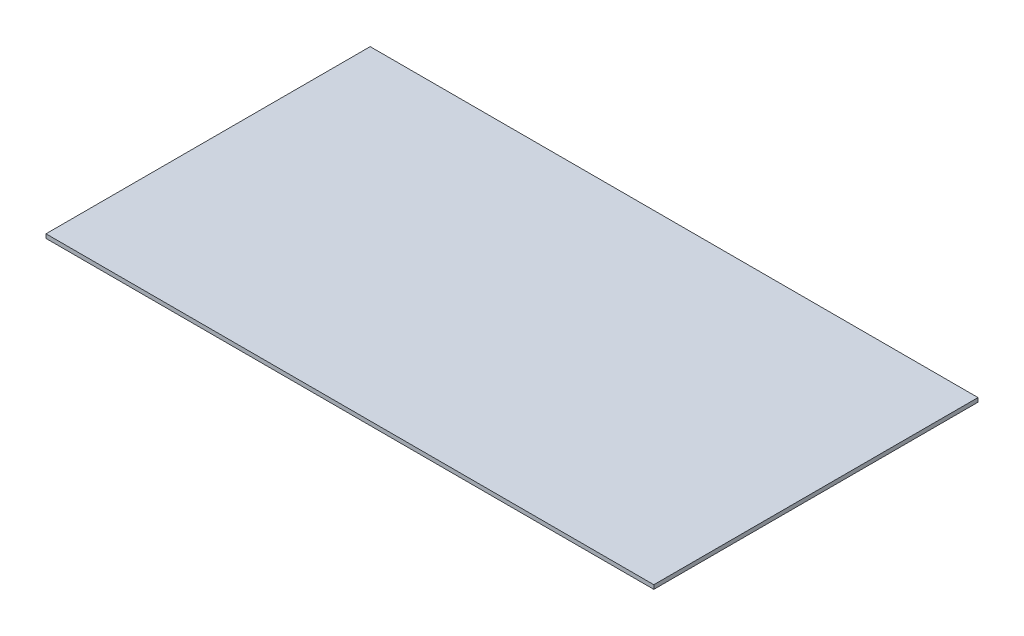
SolidWorks part; units mm, degrees
ref_plane "Front Plane" through (0, 0, 0) normal (0, 0, 1) x (1, 0, 0)
ref_plane "Top Plane" through (0, 0, 0) normal (0, 1, 0) x (1, 0, 0)
ref_plane "Right Plane" through (0, 0, 0) normal (1, 0, 0) x (0, 0, -1)
sketch "Sketch1" plane through (0, 0, 0) normal (0, 1, 0) x (1, 0, 0)
  line L1 (-75, -40) -> (75, -40)
  line L2 (-75, -40) -> (-75, 40)
  line L3 (-75, 40) -> (75, 40)
  line L4 (75, -40) -> (75, 40)
  line L5 (-75, -40) -> (75, 40) construction
  line L6 (-75, 40) -> (75, -40) construction
  point P0 (0, 0)
  dimension "D1" = 80
  dimension "D2" = 150
extrude "Boss-Extrude1" add sketch "Sketch1" along normal blind 1
